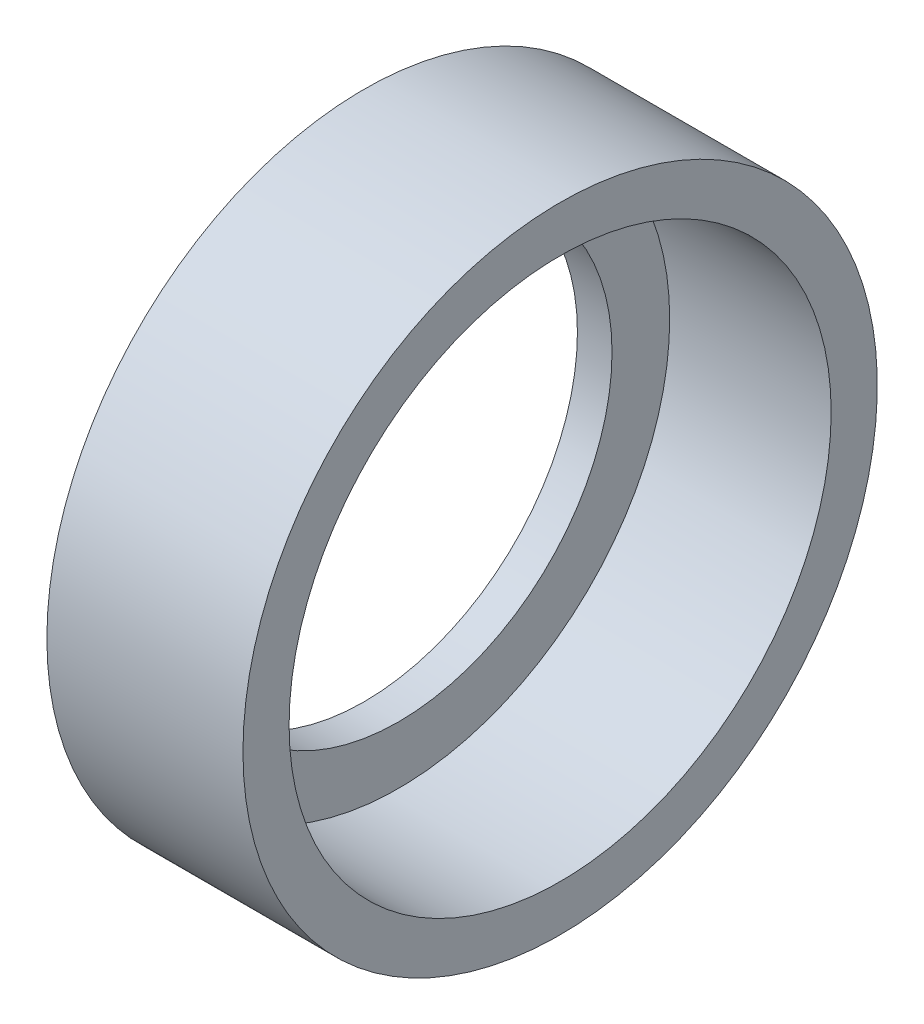
SolidWorks part; units mm, degrees
material "AISI 1020"
ref_plane "Спереди" through (0, 0, 0) normal (0, 0, 1) x (1, 0, 0)
ref_plane "Сверху" through (0, 0, 0) normal (0, 1, 0) x (1, 0, 0)
ref_plane "Справа" through (0, 0, 0) normal (1, 0, 0) x (0, 0, -1)
sketch "Эскиз1" plane through (0, 0, 0) normal (0, 1, 0) x (1, 0, 0)
  line L0 (-1000, 0) -> (49000, 0) construction
  line L1 (0, 23.5) -> (-14, 23.5)
  line L2 (-14, 23.5) -> (-14, 18.5)
  line L3 (-14, 18.5) -> (-17, 18.5)
  line L4 (-17, 18.5) -> (-17, 27.5)
  line L5 (-17, 27.5) -> (0, 27.5)
  line L6 (0, 27.5) -> (0, 23.5)
  line L7 (-11.6667, 18.5) -> (-14, 18.5) construction
  line L8 (-14, 22) -> (-14, -22) construction
  line L9 (-1.5, 23.5) -> (-12.5, 23.5) construction
  line L10 (0, -22) -> (0, 22) construction
  dimension "D1" = 3
  dimension "D2" = 55
revolve "Повернуть1" add sketch "Эскиз1" angle 360 about L0
